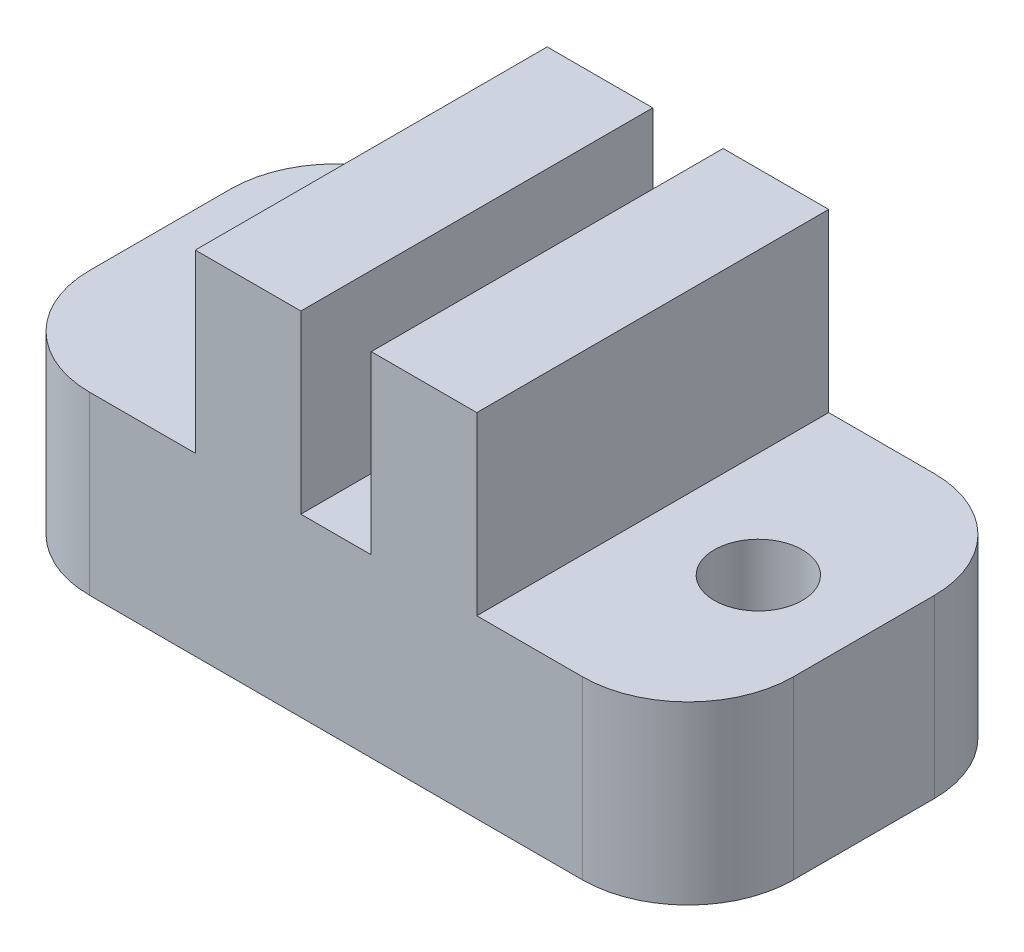
SolidWorks part; units mm, degrees
ref_plane "Front Plane" through (0, 0, 0) normal (0, 0, 1) x (1, 0, 0)
ref_plane "Top Plane" through (0, 0, 0) normal (0, 1, 0) x (1, 0, 0)
ref_plane "Right Plane" through (0, 0, 0) normal (1, 0, 0) x (0, 0, -1)
sketch "Sketch1" plane through (0, 0, 0) normal (0, 1, 0) x (1, 0, 0)
  line L1 (0, 0) -> (20, 0)
  line L2 (0, 0) -> (0, 10)
  line L3 (0, 10) -> (20, 10)
  line L4 (20, 0) -> (20, 10)
  circle A0 centre (3, 5) radius 1.25
  circle A1 centre (17, 5) radius 1.25
  point P9 (0, 5)
  dimension "D3" = 2.5
  dimension "D1" = 10
  dimension "D2" = 20
  dimension "D4" = 3
  dimension "D5" = 3
extrude "Boss-Extrude1" add sketch "Sketch1" along normal blind 5
sketch "Sketch2" plane through (0, 5, 0) normal (0, 1, 0) x (1, 0, 0)
  line L0 (20, 10) -> (0, 10) construction
  line L1 (6, 10) -> (9, 10)
  line L2 (6, 10) -> (6, 0)
  line L3 (6, 0) -> (9, 0)
  line L4 (9, 10) -> (9, 0)
  line L5 (0, 0) -> (20, 0) construction
  line L6 (9, 5) -> (11, 5) construction
  line L7 (11, 10) -> (14, 10)
  line L8 (11, 10) -> (11, 0)
  line L9 (11, 0) -> (14, 0)
  line L10 (14, 10) -> (14, 0)
  point P12 (10, 10)
  point P15 (10, 5)
  dimension "D1" = 3
  dimension "D2" = 2
extrude "Boss-Extrude2" add sketch "Sketch2" along normal blind 5
fillet "Fillet1" radius 3 4 edges at (0, 2.5, -10) (20, 2.5, -10) (0, 2.5, 0) (20, 2.5, 0)
